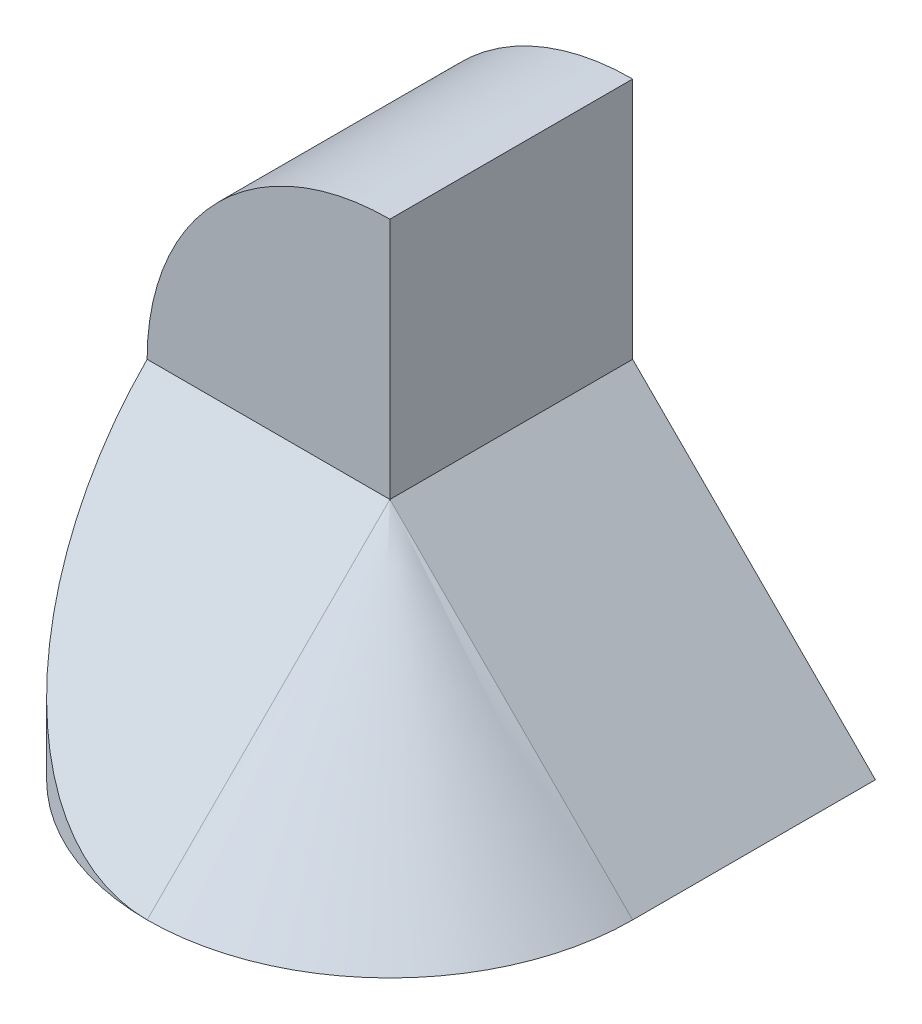
SolidWorks part; units mm, degrees
ref_plane "Front" through (0, 0, 0) normal (0, 0, 1) x (1, 0, 0)
ref_plane "Top" through (0, 0, 0) normal (0, 1, 0) x (1, 0, 0)
ref_plane "Right" through (0, 0, 0) normal (1, 0, 0) x (0, 0, -1)
sketch "Sketch1" plane through (0, 0, 0) normal (0, 0, 1) x (1, 0, 0)
  line L0 (0, 0) -> (2, 0)
  line L5 (2, 0) -> (2, 4)
  line L7 (0, 2) -> (0, 0)
  arc A0 (2, 4) -> (0, 2) centre (2, 2) ccw
  dimension "D1" = 2
  dimension "D2" = 4
  dimension "D3" = 2
  dimension "D4" = 2
extrude "Boss-Extrude1" add sketch "Sketch1" along normal blind 2
sketch "Sketch3" plane through (0, 0, 2) normal (0, 0, 1) x (1, 0, 0)
  line L0 (2, 2) -> (2, 0) construction
  line L1 (2, 0) -> (2, 4) construction
  line L2 (2, 2) -> (4, 0)
  line L3 (4, 0) -> (2, 0)
  line L4 (2, 0) -> (2, 2)
  dimension "D1" = 2
  dimension "D2" = 2
revolve "Revolve1" add sketch "Sketch3" angle 90 about L0
sketch "Sketch4" plane through (2, 0, 0) normal (-1, 0, 0) x (0, 0, 1)
  line L0 (2, 2) -> (2, 0)
  line L1 (2, 0) -> (4, 0)
  line L2 (4, 0) -> (2, 2)
  point P6 (0, 0)
  point P7 (0, 0)
  point P8 (0, 0)
extrude "Boss-Extrude2" add sketch "Sketch4" along normal blind 2
sketch "Sketch5" plane through (0, 0, 0) normal (0, -1, 0) x (1, 0, 0)
  line L1 (2, 4) -> (0, 4)
  line L2 (0, 4) -> (0, 2)
  arc A0 (0, 2) -> (2, 4) centre (2, 2) cw
  arc A1 (4, 2) -> (2, 4) centre (2, 2) ccw construction
  point P3 (0, 0)
extrude "Cut-Extrude1" cut sketch "Sketch5" against normal blind 2
sketch "Sketch7" plane through (0, 0, 0) normal (0, 0, -1) x (-1, 0, 0)
  line L1 (-2, 0) -> (0, 0)
  line L2 (0, 0) -> (0, 2)
  arc A0 (0, 2) -> (-2, 0) centre (-2, 2) cw
extrude "Cut-Extrude2" cut sketch "Sketch7" against normal blind 1
sketch "Sketch8" plane through (0, 0, 2) normal (0, 0, -1) x (-1, 0, 0)
  line L0 (-2, 2) -> (-2, 0)
  line L1 (-2, 0) -> (-4, 0)
  line L2 (-4, 0) -> (-2, 2)
extrude "Boss-Extrude3" add sketch "Sketch8" along normal blind 2
